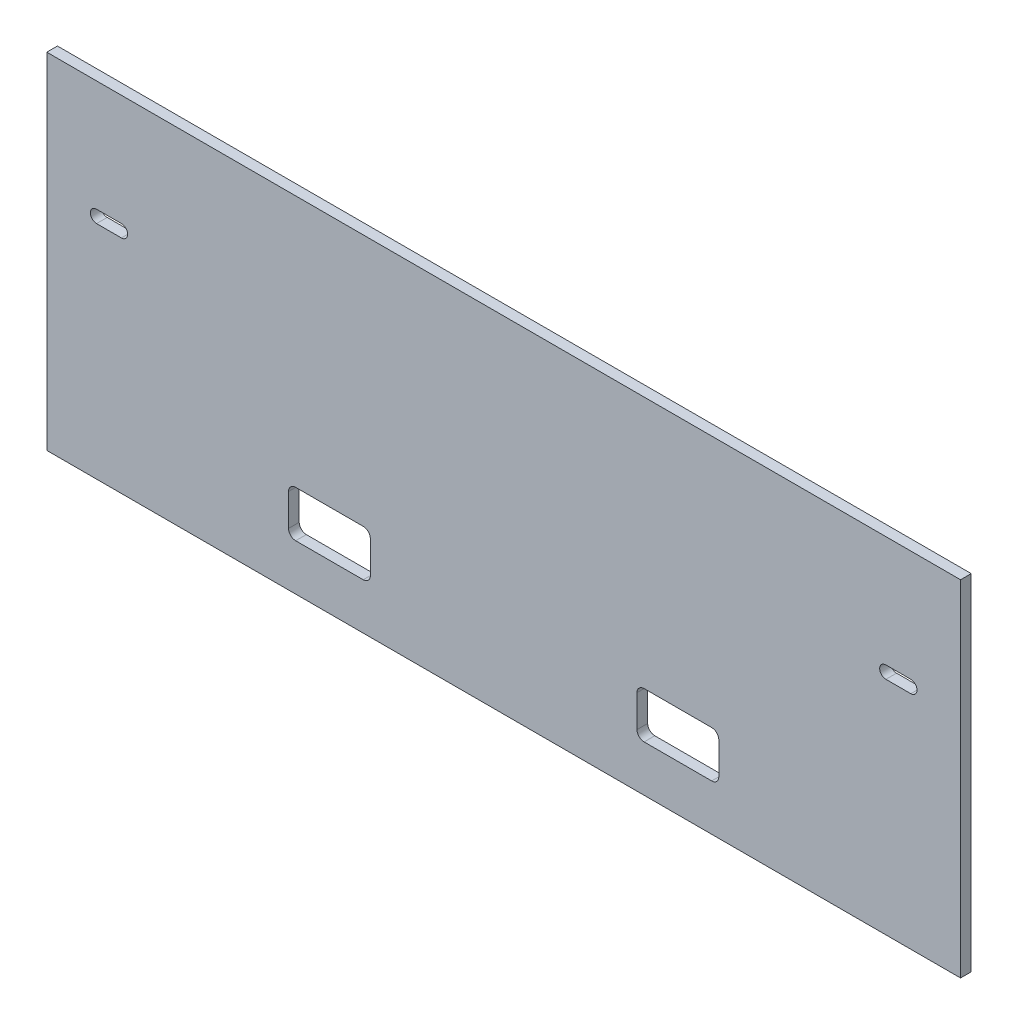
SolidWorks part; units mm, degrees
ref_plane "Plan de face" through (0, 0, 0) normal (0, 0, 1) x (1, 0, 0)
ref_plane "Plan de dessus" through (0, 0, 0) normal (0, 1, 0) x (1, 0, 0)
ref_plane "Plan de droite" through (0, 0, 0) normal (1, 0, 0) x (0, 0, -1)
sketch "Esquisse1" plane through (0, 0, 0) normal (0, 0, 1) x (1, 0, 0)
  line L0 (0, 48.5) -> (0, -48.5) construction
  line L1 (128.5, 48.5) -> (-128.5, 48.5)
  line L2 (128.5, 48.5) -> (128.5, -48.5)
  line L3 (128.5, -48.5) -> (-128.5, -48.5)
  line L4 (-128.5, 48.5) -> (-128.5, -48.5)
  line L5 (128.5, 48.5) -> (-128.5, -48.5) construction
  line L6 (128.5, -48.5) -> (-128.5, 48.5) construction
  line L7 (-111, 15.5) -> (0, 15.5) construction
  line L8 (-114.5, 15.5) -> (-107.5, 15.5) construction
  line L9 (-114.5, 17.25) -> (-107.5, 17.25)
  line L10 (-114.5, 13.75) -> (-107.5, 13.75)
  line L11 (107.5, 15.5) -> (114.5, 15.5) construction
  line L12 (107.5, 17.25) -> (114.5, 17.25)
  line L13 (107.5, 13.75) -> (114.5, 13.75)
  circle A0 centre (-111, 15.5) radius 1.75 construction
  circle A1 centre (111, 15.5) radius 1.75 construction
  arc A2 (-114.5, 17.25) -> (-114.5, 13.75) centre (-114.5, 15.5) ccw
  arc A3 (-107.5, 13.75) -> (-107.5, 17.25) centre (-107.5, 15.5) ccw
  arc A4 (107.5, 17.25) -> (107.5, 13.75) centre (107.5, 15.5) ccw
  arc A5 (114.5, 13.75) -> (114.5, 17.25) centre (114.5, 15.5) ccw
  point P0 (0, 0)
  point P15 (-111, 15.5)
  point P22 (111, 15.5)
  dimension "D3" = 3.5
  dimension "D7" = 1.75
  dimension "D9" = 1.75
  dimension "D1" = 257
  dimension "D2" = 97
  dimension "D4" = 111
  dimension "D5" = 33
  dimension "D6" = 7
  dimension "D8" = 7
extrude "Boss.-Extru.1" add sketch "Esquisse1" along normal blind 3
sketch "Esquisse2" plane through (0, 0, 3) normal (0, 0, 1) x (1, 0, 0)
  line L0 (-37.5, -35.5) -> (37.5, -35.5) construction
  line L1 (-60.5, -35.5) -> (-37.5, -35.5)
  line L2 (-60.5, -35.5) -> (-60.5, -22.5)
  line L3 (-60.5, -22.5) -> (-37.5, -22.5)
  line L4 (-37.5, -35.5) -> (-37.5, -22.5)
  line L5 (37.5, -35.5) -> (60.5, -35.5)
  line L6 (37.5, -35.5) -> (37.5, -22.5)
  line L7 (37.5, -22.5) -> (60.5, -22.5)
  line L8 (60.5, -35.5) -> (60.5, -22.5)
  line L9 (0, 0) -> (0, -35.5) construction
  line L10 (-128.5, -48.5) -> (128.5, -48.5) construction
  point P8 (-49, -22.5)
  point P9 (49, -22.5)
  dimension "D1" = 98
  dimension "D2" = 23
  dimension "D3" = 13
  dimension "D4" = 13
extrude "Enlèv. mat.-Extru.1" cut sketch "Esquisse2" against normal up to next
fillet "Congé1" radius 2 8 edges at (37.5, -35.5, 1.5) (60.5, -35.5, 1.5) (60.5, -22.5, 1.5) (37.5, -22.5, 1.5) (-60.5, -35.5, 1.5) (-37.5, -35.5, 1.5) (-37.5, -22.5, 1.5) (-60.5, -22.5, 1.5)
